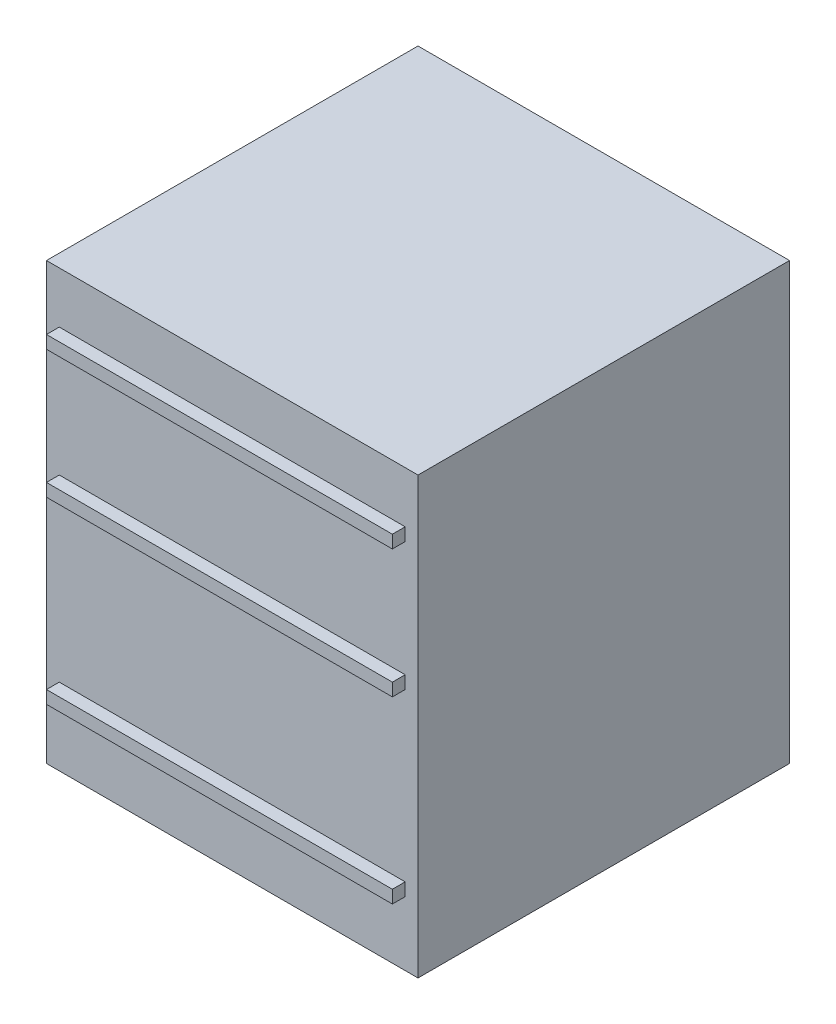
SolidWorks part; units mm, degrees
ref_plane "Front Plane" through (0, 0, 0) normal (0, 0, 1) x (1, 0, 0)
ref_plane "Top Plane" through (0, 0, 0) normal (0, 1, 0) x (1, 0, 0)
ref_plane "Right Plane" through (0, 0, 0) normal (1, 0, 0) x (0, 0, -1)
sketch "Sketch1" plane through (0, 0, 0) normal (0, 1, 0) x (1, 0, 0)
  line L1 (-368.3, -368.3) -> (368.3, -368.3)
  line L2 (-368.3, -368.3) -> (-368.3, 368.3)
  line L3 (-368.3, 368.3) -> (368.3, 368.3)
  line L4 (368.3, -368.3) -> (368.3, 368.3)
  line L5 (-368.3, -368.3) -> (368.3, 368.3) construction
  line L6 (-368.3, 368.3) -> (368.3, -368.3) construction
  point P0 (0, 0)
  dimension "D1" = 736.6
  dimension "D2" = 736.6
extrude "Boss-Extrude1" add sketch "Sketch1" along normal blind 863.6
sketch "Sketch2" plane through (0, 0, 368.3) normal (0, 0, 1) x (1, 0, 0)
  line L0 (-368.3, 863.6) -> (-368.3, 0) construction
  line L1 (-342.9, 762) -> (342.9, 762)
  line L2 (-342.9, 762) -> (-342.9, 736.6)
  line L3 (-342.9, 736.6) -> (342.9, 736.6)
  line L4 (342.9, 762) -> (342.9, 736.6)
  line L5 (-342.9, 508) -> (342.9, 508)
  line L6 (-342.9, 508) -> (-342.9, 482.6)
  line L7 (-342.9, 482.6) -> (342.9, 482.6)
  line L8 (342.9, 508) -> (342.9, 482.6)
  line L9 (-342.9, 152.4) -> (342.9, 152.4)
  line L10 (-342.9, 152.4) -> (-342.9, 127)
  line L11 (-342.9, 127) -> (342.9, 127)
  line L12 (342.9, 152.4) -> (342.9, 127)
  line L13 (368.3, 863.6) -> (368.3, 0) construction
  line L14 (-368.3, 863.6) -> (368.3, 863.6) construction
  dimension "D1" = 25.4
  dimension "D2" = 25.4
  dimension "D3" = 25.4
  dimension "D4" = 101.6
  dimension "D5" = 228.6
  dimension "D6" = 330.2
extrude "Boss-Extrude2" add sketch "Sketch2" along normal blind 25.4
